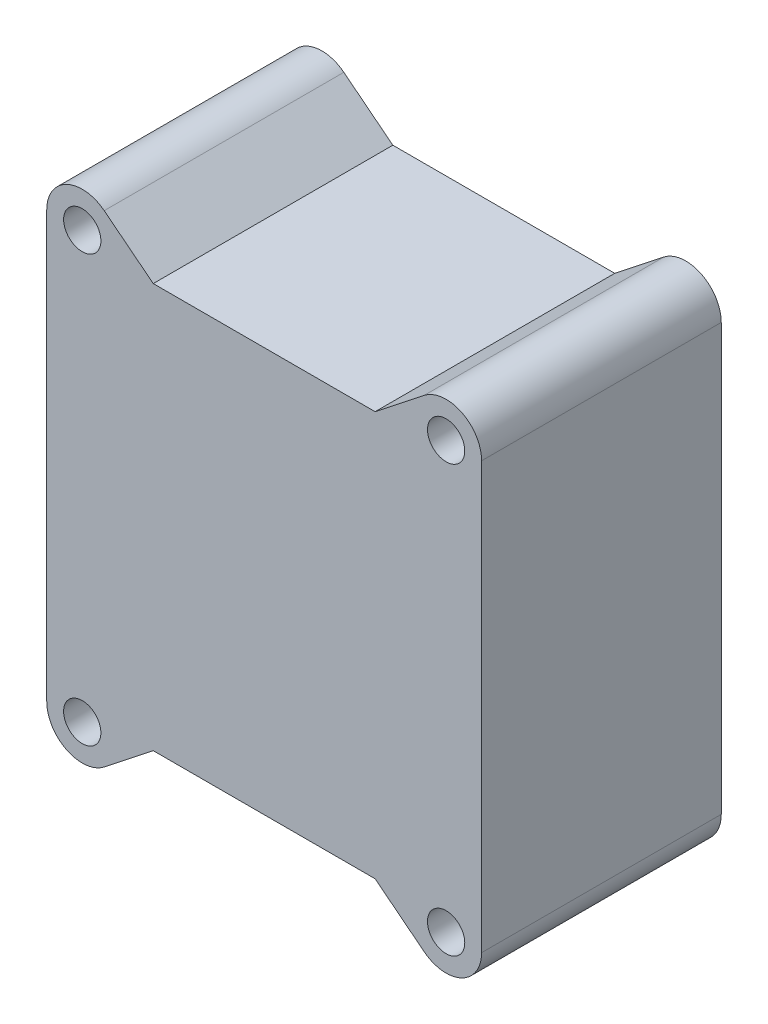
SolidWorks part; units mm, degrees
ref_plane "Ebene vorne" through (0, 0, 0) normal (0, 0, 1) x (1, 0, 0)
ref_plane "Ebene oben" through (0, 0, 0) normal (0, 1, 0) x (1, 0, 0)
ref_plane "Ebene rechts" through (0, 0, 0) normal (1, 0, 0) x (0, 0, -1)
sketch "Skizze1" plane through (0, 0, 0) normal (0, 0, 1) x (1, 0, 0)
  line L0 (0, 14.7424) -> (0, 3.25) construction
  line L1 (0, 3.25) -> (17.0168, 3.25) construction
  circle A0 centre (10.5, -3.5) radius 3
  circle A1 centre (10.5, 10) radius 3
  circle A2 centre (-10.5, 10) radius 3
  circle A3 centre (-10.5, -3.5) radius 3
  dimension "D1" = 6
extrude "Aufsatz Kamera Halterung" add sketch "Skizze1" along normal blind 3
sketch "Skizze2" plane through (0, 0, 3) normal (0, 0, 1) x (1, 0, 0)
  line L1 (21.5, -16) -> (-21.5, -16)
  line L2 (21.5, -16) -> (21.5, 24)
  line L3 (21.5, 24) -> (-21.5, 24)
  line L4 (-21.5, -16) -> (-21.5, 24)
  line L5 (21.5, -16) -> (-21.5, 24) construction
  line L6 (21.5, 24) -> (-21.5, -16) construction
  line L9 (21.5, 24) -> (-21.5, 24) construction
  line L10 (-21.5, 24) -> (-21.5, -16) construction
  point P0 (0, 4)
extrude "Deckel" add sketch "Skizze2" along normal blind 3
sketch "Skizze3" plane through (0, 0, 0) normal (0, 0, -1) x (-1, 0, 0)
  line L0 (0, 21.657) -> (0, 3.25) construction
  line L1 (0, 3.25) -> (21.3456, 3.25) construction
  circle A0 centre (10.5, 10) radius 1.7
  circle A1 centre (10.5, -3.5) radius 1.7
  circle A2 centre (-10.5, -3.5) radius 1.7
  circle A3 centre (-10.5, 10) radius 1.7
  dimension "D1" = 3.4
extrude "Löcher Kamera Halterung" cut sketch "Skizze3" against normal blind 4
sketch "Skizze4" plane through (0, 0, 6) normal (0, 0, 1) x (1, 0, 0)
  line L1 (21.5, -16) -> (-21.5, -16)
  line L2 (21.5, -16) -> (21.5, 24)
  line L3 (21.5, 24) -> (-21.5, 24)
  line L4 (-21.5, -16) -> (-21.5, 24)
  line L5 (21.5, -16) -> (-21.5, 24) construction
  line L6 (21.5, 24) -> (-21.5, -16) construction
  line L7 (24.5, -18.7907) -> (-24.5, -18.7907)
  line L8 (24.5, -18.7907) -> (24.5, 26.7907)
  line L9 (24.5, 26.7907) -> (-24.5, 26.7907)
  line L10 (-24.5, -18.7907) -> (-24.5, 26.7907)
  line L11 (24.5, -18.7907) -> (-24.5, 26.7907) construction
  line L12 (24.5, 26.7907) -> (-24.5, -18.7907) construction
  point P0 (0, 4)
  point P8 (0, 4)
  dimension "D1" = 3
extrude "Aufsatz-Linear austragen1" add sketch "Skizze4" against normal up to surface (27 mm away)
sketch "Skizze5" plane through (0, -18.7907, 0) normal (0, -1, 0) x (-1, 0, 0)
  line L1 (4.1136, -3.42) -> (-27.7667, -3.42)
  line L2 (4.1136, -3.42) -> (4.1136, 68.3619)
  line L3 (4.1136, 68.3619) -> (-27.7667, 68.3619)
  line L4 (-27.7667, -3.42) -> (-27.7667, 68.3619)
sketch "Skizze6" plane through (0, -18.7907, 0) normal (0, -1, 0) x (-1, 0, 0)
  line L0 (0, -3) -> (0, 3.5) construction
  line L1 (12.5, 0.5) -> (-12.5, 0.5)
  line L2 (12.5, 0.5) -> (12.5, 3.5)
  line L3 (12.5, 3.5) -> (-12.5, 3.5)
  line L4 (-12.5, 0.5) -> (-12.5, 3.5)
  line L5 (21.5, -3) -> (-21.5, -3) construction
  dimension "D1" = 25
  dimension "D2" = 3
  dimension "D3" = 3.5
extrude "Schnitt-Linear austragen1" cut sketch "Skizze6" against normal up to surface (2.7907 mm away) up to face at (0, -16, -9)
sketch "Skizze7" plane through (0, 0, -21) normal (0, 0, -1) x (-1, 0, 0)
  line L0 (21.5, 24) -> (-21.5, 24) construction
  line L1 (0, 26.7907) -> (0, 4) construction
  line L2 (24.5, 26.7907) -> (-24.5, 26.7907) construction
  line L3 (0, 4) -> (24.5, 4) construction
  line L4 (24.5, -18.7907) -> (24.5, 26.7907) construction
  line L5 (-24.5, 26.7907) -> (-24.5, -18.7907) construction
  circle A0 centre (-20.5, 28) radius 4
  circle A1 centre (20.5, 28) radius 4
  circle A2 centre (20.5, -20) radius 4
  circle A3 centre (-20.5, -20) radius 4
  dimension "D1" = 8
extrude "Aufsatz-Linear austragen2" add sketch "Skizze7" against normal through all
sketch "Skizze8" plane through (0, 0, -21) normal (0, 0, -1) x (-1, 0, 0)
  line L0 (0, 26.7907) -> (0, 4) construction
  line L1 (16.6872, 26.7907) -> (-16.6872, 26.7907) construction
  line L2 (0, 4) -> (24.5, 4) construction
  line L3 (24.5, -18.7907) -> (24.5, 26.7907) construction
  circle A0 centre (-20.5, 28) radius 2.1
  circle A1 centre (20.5, 28) radius 2.1
  circle A2 centre (20.5, -20) radius 2.1
  circle A3 centre (-20.5, -20) radius 2.1
  dimension "D1" = 4.2
extrude "Schnitt-Linear austragen2" cut sketch "Skizze8" against normal blind 5.7
sketch "Skizze9" plane through (0, 0, -21) normal (0, 0, -1) x (-1, 0, 0)
  line L0 (0, 26.7907) -> (0, 4) construction
  line L1 (-24.5, 26.7907) -> (-24.3128, 26.7907)
  line L2 (-24.5, 26.7907) -> (-24.5, 28)
  line L3 (-24.5, 28) -> (-24.3128, 28)
  line L4 (-24.3128, 26.7907) -> (-24.3128, 28)
  line L5 (16.6872, 26.7907) -> (-16.6872, 26.7907) construction
  line L6 (0, 4) -> (24.5, 4) construction
  line L7 (24.5, -18.7907) -> (24.5, 26.7907) construction
  line L8 (24.3128, 26.7907) -> (24.3128, 28)
  line L9 (24.5, 28) -> (24.3128, 28)
  line L10 (24.5, 26.7907) -> (24.5, 28)
  line L11 (24.5, 26.7907) -> (24.3128, 26.7907)
  line L12 (24.5, -18.7907) -> (24.3128, -18.7907)
  line L13 (24.5, -18.7907) -> (24.5, -20)
  line L14 (24.5, -20) -> (24.3128, -20)
  line L15 (24.3128, -18.7907) -> (24.3128, -20)
  line L16 (-24.3128, -18.7907) -> (-24.3128, -20)
  line L17 (-24.5, -20) -> (-24.3128, -20)
  line L18 (-24.5, -18.7907) -> (-24.5, -20)
  line L19 (-24.5, -18.7907) -> (-24.3128, -18.7907)
  line L36 (-18.025, 31.1423) -> (-12.5, 26.7907)
  line L37 (-12.5, 26.7907) -> (-16.6872, 26.7907)
  line L39 (12.5, 26.7907) -> (16.6872, 26.7907)
  line L40 (18.025, 31.1423) -> (12.5, 26.7907)
  line L41 (18.025, -23.1423) -> (12.5, -18.7907)
  line L42 (12.5, -18.7907) -> (16.6872, -18.7907)
  line L43 (-12.5, -18.7907) -> (-16.6872, -18.7907)
  line L44 (-18.025, -23.1423) -> (-12.5, -18.7907)
  arc A0 (-16.6872, 26.7907) -> (-24.3128, 26.7907) centre (-20.5, 28) ccw construction
  arc A1 (-18.025, 31.1423) -> (-16.6872, 26.7907) centre (-20.5, 28) cw
  arc A2 (18.025, 31.1423) -> (16.6872, 26.7907) centre (20.5, 28) ccw
  arc A3 (18.025, -23.1423) -> (16.6872, -18.7907) centre (20.5, -20) cw
  arc A4 (-18.025, -23.1423) -> (-16.6872, -18.7907) centre (-20.5, -20) ccw
extrude "Aufsatz-Linear austragen3" add sketch "Skizze9" against normal through all
sketch "Skizze10" plane through (0, 0, 6) normal (0, 0, 1) x (1, 0, 0)
  line L0 (0, 29.144) -> (0, 4) construction
  line L1 (0, 4) -> (40.9063, 4) construction
  circle A0 centre (-20.5, 28) radius 2.1
  circle A1 centre (20.5, 28) radius 2.1
  circle A2 centre (20.5, -20) radius 2.1
  circle A3 centre (-20.5, -20) radius 2.1
  dimension "D1" = 4.2
extrude "Schnitt-Linear austragen3" cut sketch "Skizze10" against normal blind 5.7
sketch "Skizze11" plane through (-24.5, 0, 0) normal (-1, 0, 0) x (0, 0, 1)
  circle A0 centre (-15.2, -14.85) radius 3
  dimension "D1" = 6
extrude "Aufsatz-Linear austragen4" add sketch "Skizze11" along normal up to surface (6 mm away)
sketch "Skizze12" plane through (-30.5, 0, 0) normal (-1, 0, 0) x (0, 0, 1)
  circle A0 centre (-15.2, -14.85) radius 1.7
  dimension "D1" = 3.4
extrude "Schnitt-Linear austragen4" cut sketch "Skizze12" against normal blind 4
chamfer "Fase1" distance 2 angle 70 1 edges at (-24.5, -14.85, -12.2)
equation "\"M2EinschmelzGewindeDurchmesser\"=3.4"
equation "\"M2EinschmelzGewindeTiefe\"= 4"
equation "\"M3EinschmelzGewindeDurchmesser\"= 4.2"
equation "\"M3EinschmelzGewindeTief\"= 5.7"
equation "\"D1@Skizze3\"=\"M2EinschmelzGewindeDurchmesser\""
equation "\"D1@Löcher Kamera Halterung\" = \"M2EinschmelzGewindeTiefe\""
equation "\"M2SchraubeLoch\"=2.3"
equation "\"D1@Skizze8\"=\"M3EinschmelzGewindeDurchmesser\""
equation "\"D1@Schnitt-Linear austragen2\"=\"M3EinschmelzGewindeTief\""
equation "\"D1@Skizze10\"=\"M3EinschmelzGewindeDurchmesser\""
equation "\"D1@Schnitt-Linear austragen3\"=\"M3EinschmelzGewindeTief\""
equation "\"D1@Skizze12\"=\"M2EinschmelzGewindeDurchmesser\""
equation "\"D1@Schnitt-Linear austragen4\"=\"M2EinschmelzGewindeTiefe\""
